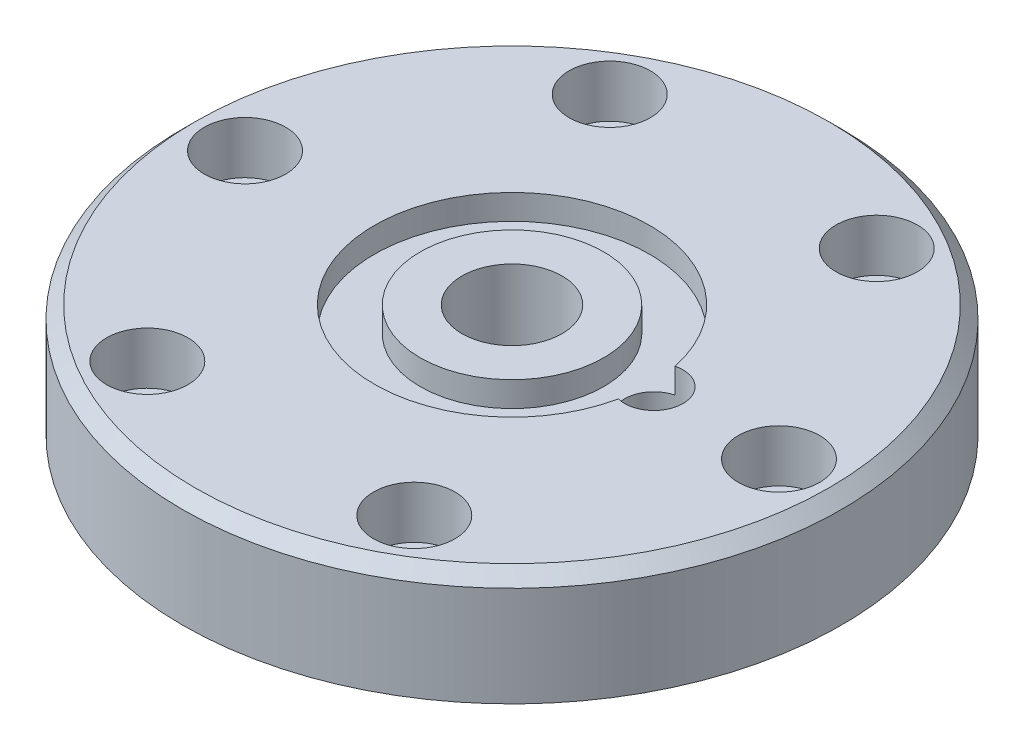
SolidWorks part; units mm, degrees
ref_plane "Front Plane" through (0, 0, 0) normal (0, 0, 1) x (1, 0, 0)
ref_plane "Top Plane" through (0, 0, 0) normal (0, 1, 0) x (1, 0, 0)
ref_plane "Right Plane" through (0, 0, 0) normal (1, 0, 0) x (0, 0, -1)
sketch "Sketch1" plane through (0, 0, 0) normal (0, 1, 0) x (1, 0, 0)
  circle A0 centre (0, 0) radius 79
  circle A1 centre (0, 0) radius 12
extrude "Boss-Extrude3" add sketch "Sketch1" along normal blind 27
hole_wizard "CBORE for #00 Binding Head Machine Screw1" positions "Sketch4" profile "Sketch5" counterbore size "#00" standard "ANSI Inch" end condition through all
sketch "Sketch4" plane through (0, 27, 0) normal (0, 1, 0) x (1, 0, 0)
  line L0 (0, 0) -> (32, 55.4256) construction
  circle A0 centre (0, 0) radius 64 construction
  point P0 (32, 55.4256)
  point P22 (64, 0)
  point P23 (32, -55.4256)
  point P24 (-32, -55.4256)
  point P25 (-64, 0)
  point P26 (-32, 55.4256)
  point P27 (0, 0)
  dimension "D1" = 6
sketch "Sketch5" plane through (32, 27, -55.4256) normal (1, 0, 0) x (0, 0, 1)
  line L0 (0, 0) -> (0, 27)
  line L1 (0, 27) -> (6.25, 27)
  line L3 (6.25, 27) -> (6.25, 12.5)
  line L4 (6.25, 12.5) -> (9.75, 12.5)
  line L5 (9.75, 12.5) -> (9.75, 0)
  line L7 (9.75, 0) -> (0, 0)
  line L11 (0, -6.35) -> (0, 107.95) construction
  dimension "Thru Hole Dia." = 12.5
  dimension "Thru Hole Depth" = 27
  dimension "C'Bore Dia." = 19.5
  dimension "C'Bore Depth" = 12.5
hole_wizard "#97 (0.0059) Diameter Hole1" positions "Sketch6" profile "Sketch7" hole size "#97" standard "ANSI Inch"
sketch "Sketch6" plane through (0, 27, 0) normal (0, 1, 0) x (1, 0, 0)
  line L0 (-14.85, 0) -> (14.85, 0) construction
  point P0 (34, 0)
  dimension "D1" = 34
sketch "Sketch7" plane through (34, 27, 0) normal (1, 0, 0) x (0, 0, 1)
  line L0 (0, 0) -> (0, 21.206)
  line L1 (0, 21.206) -> (7, 17)
  line L2 (7, 17) -> (7, 0)
  line L5 (7, 0) -> (0, 0)
  line L10 (0, 21.206) -> (-7, 17) construction
  line L11 (0, -6.35) -> (0, 107.95) construction
  dimension "Hole Dia." = 14
  dimension "Hole Depth" = 17
  dimension "Drill Angle" = 118
sketch "Sketch8" plane through (0, 27, 0) normal (0, 1, 0) x (1, 0, 0)
  circle A0 centre (0, 0) radius 22
  circle A1 centre (0, 0) radius 33
  circle A2 centre (0, 0) radius 79 construction
  dimension "D1" = 46
  dimension "D2" = 11
extrude "Cut-Extrude1" cut sketch "Sketch8" against normal blind 6
chamfer "Chamfer1" distance 3 angle 45 1 edges at (0, 27, 79)
